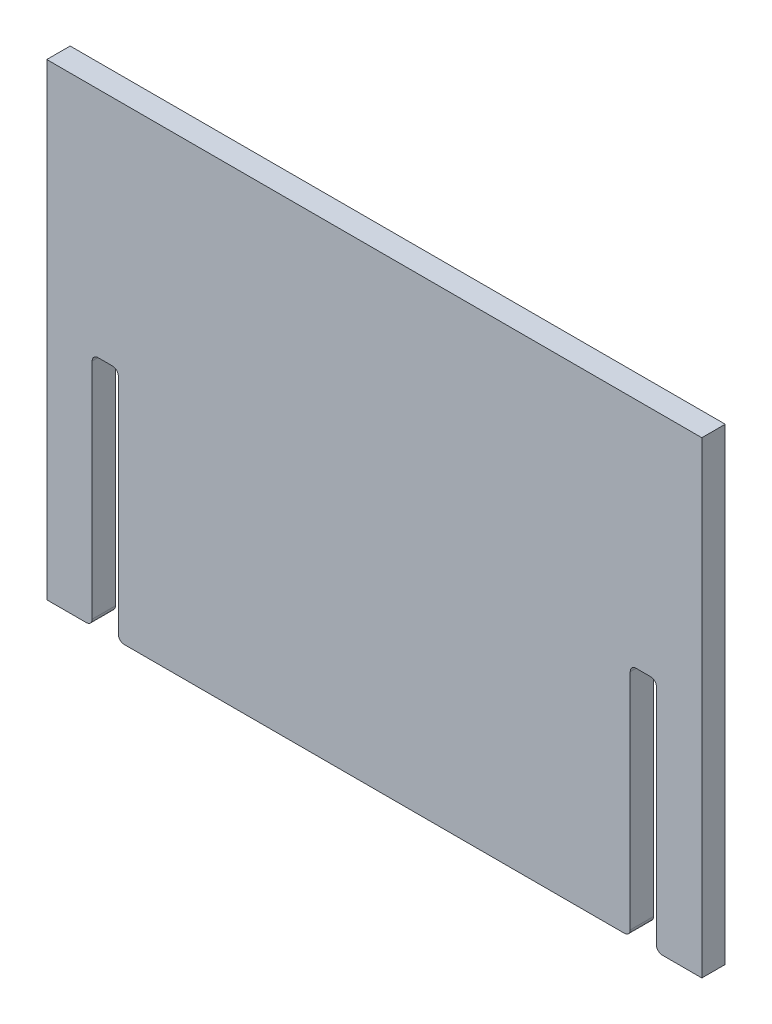
SolidWorks part; units mm, degrees
ref_plane "Front Plane" through (0, 0, 0) normal (0, 0, 1) x (1, 0, 0)
ref_plane "Top Plane" through (0, 0, 0) normal (0, 1, 0) x (1, 0, 0)
ref_plane "Right Plane" through (0, 0, 0) normal (1, 0, 0) x (0, 0, -1)
sketch "Sketch1" plane through (0, 0, 0) normal (0, 0, 1) x (1, 0, 0)
  line L7 (1294.204, -519.4799) -> (1294.204, -532.1799) construction
  line L8 (1294.204, -24.1799) -> (1649.804, -24.1799)
  line L9 (1294.204, -24.1799) -> (1294.204, -278.1799)
  line L11 (1649.804, -24.1799) -> (1649.804, -278.1799)
  line L12 (1649.804, -519.4799) -> (1649.804, -532.1799) construction
  line L13 (1332.304, -24.1799) -> (1319.604, -24.1799) construction
  line L14 (1294.204, -278.1799) -> (1319.604, -278.1799)
  line L15 (1319.604, -24.1799) -> (1319.604, -519.4799) construction
  line L16 (1319.604, -278.1799) -> (1319.604, -151.1799)
  line L17 (1319.604, -151.1799) -> (1332.304, -151.1799)
  line L18 (1332.304, -24.1799) -> (1332.304, -519.4799) construction
  line L19 (1332.304, -151.1799) -> (1332.304, -278.1799)
  line L20 (1332.304, -278.1799) -> (1611.704, -278.1799)
  line L21 (1611.704, -24.1799) -> (1611.704, -519.4799) construction
  line L22 (1611.704, -278.1799) -> (1611.704, -151.1799)
  line L23 (1611.704, -151.1799) -> (1624.404, -151.1799)
  line L24 (1624.404, -24.1799) -> (1624.404, -519.4799) construction
  line L25 (1624.404, -151.1799) -> (1624.404, -278.1799)
  line L26 (1624.404, -278.1799) -> (1649.804, -278.1799)
  dimension "D1" = 127
  dimension "D2" = 254
extrude "Boss-Extrude1" add sketch "Sketch1" along normal mid plane 12.7
other "Move Face slot" face at (1624.404, -214.6799, 0) face at (1618.054, -151.1799, 0) face at (1611.704, -214.6799, 0) face at (1319.604, -214.6799, 0) face at (1325.954, -151.1799, 0) face at (1332.304, -214.6799, 0) parameters "D1"=0.762
fillet "Fillet1" radius 3.175 8 edges at (1625.166, -278.1799, 0) (1610.942, -278.1799, 0) (1333.066, -278.1799, 0) (1318.842, -278.1799, 0) (1625.166, -150.4179, 0) (1610.942, -150.4179, 0) (1333.066, -150.4179, 0) (1318.842, -150.4179, 0)
